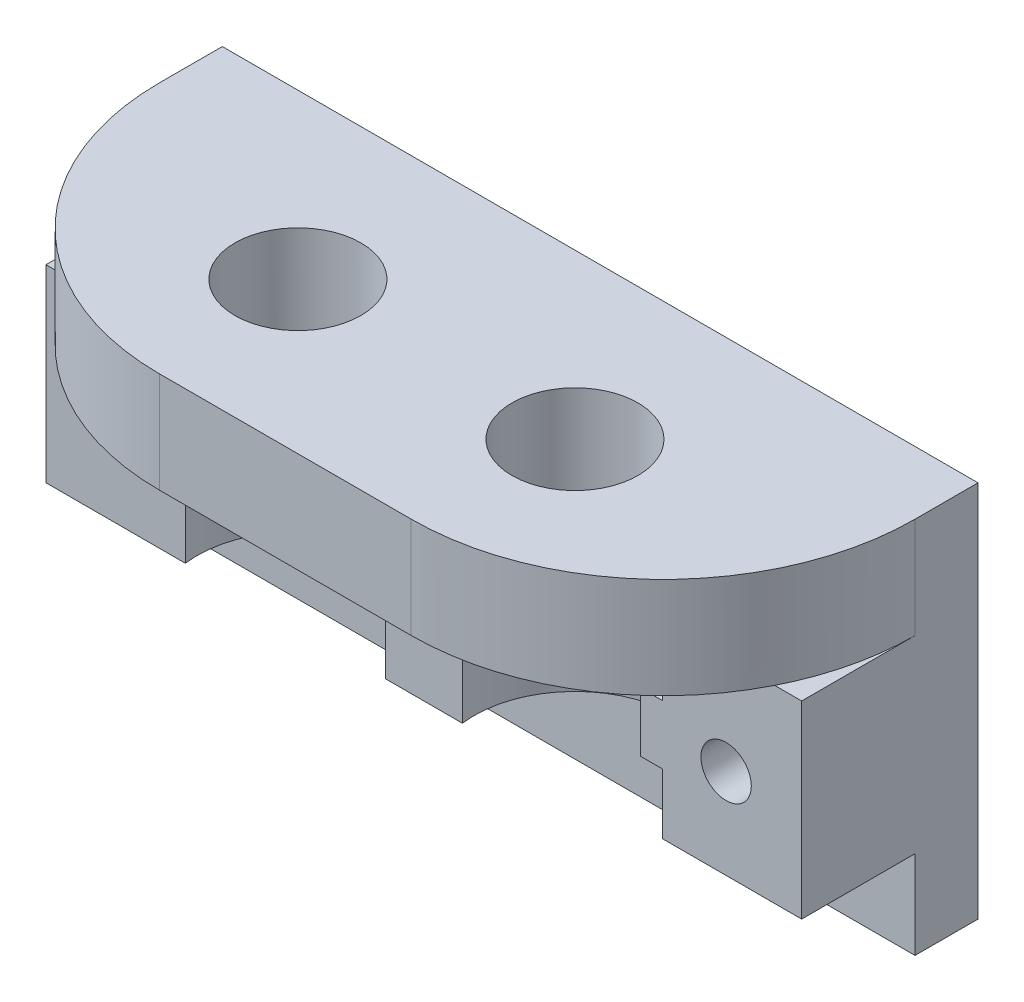
SolidWorks part; units mm, degrees
ref_plane "Piano frontale" through (0, 0, 0) normal (0, 0, 1) x (1, 0, 0)
ref_plane "Piano superiore" through (0, 0, 0) normal (0, 1, 0) x (1, 0, 0)
ref_plane "Piano destro" through (0, 0, 0) normal (1, 0, 0) x (0, 0, -1)
sketch "Schizzo1" plane through (0, 0, 0) normal (0, 0, 1) x (1, 0, 0)
  line L1 (-30, 15) -> (30, 15)
  line L2 (-30, 15) -> (-30, -15)
  line L3 (-30, -15) -> (30, -15)
  line L4 (30, 15) -> (30, -15)
  line L5 (-30, 15) -> (30, -15) construction
  line L6 (-30, -15) -> (30, 15) construction
  point P0 (0, 0)
  dimension "D1" = 60
  dimension "D2" = 30
extrude "Estrusione-Estrusione1" add sketch "Schizzo1" along normal blind 5
sketch "Schizzo2" plane through (0, 0, 5) normal (0, 0, 1) x (1, 0, 0)
  line L0 (-32.3459, -15) -> (49.5432, -15) construction
  line L1 (-32.3459, -8) -> (49.5432, -8) construction
  line L3 (30, -15) -> (30, 15) construction
  line L4 (-30, 15) -> (30, 15)
  line L5 (-30, 15) -> (-30, 7)
  line L6 (-30, 7) -> (30, 7)
  line L7 (30, 15) -> (30, 7)
  dimension "D1" = 7
extrude "Estrusione-Estrusione2" add sketch "Schizzo2" along normal blind 20
sketch "Schizzo3" plane through (0, 15, 0) normal (0, 1, 0) x (1, 0, 0)
  line L0 (0, 7.3603) -> (0, -33.3603) construction
  line L1 (11, 7.3603) -> (11, -33.3603) construction
  line L2 (30, 0) -> (-30, 0) construction
  circle A0 centre (11, -13) radius 5
  circle A1 centre (-11, -13) radius 5
  dimension "D2" = 10
  dimension "D3" = 13
  dimension "D1" = 11
extrude "Taglio-Estrusione1" cut sketch "Schizzo3" against normal up to surface (8 mm away) up to face at (-7.5, 7, 20)
fillet "Raccordo1" radius 20 2 edges at (30, 11, 25) (-30, 11, 25)
sketch "Schizzo4" plane through (0, 0, 5) normal (0, 0, 1) x (1, 0, 0)
  line L0 (-30, 7) -> (30, 7) construction
  line L1 (-30, 7) -> (30, 7)
  line L2 (-30, -8) -> (30, -8)
  line L3 (-30, -8) -> (-30, 7)
  line L4 (30, -8) -> (30, 7)
  dimension "D1" = 15
extrude "Estrusione-Estrusione3" add sketch "Schizzo4" along normal blind 10
sketch "Schizzo6" plane through (0, -8, 0) normal (0, -1, 0) x (1, 0, 0)
  line L0 (0, 28.7661) -> (0, -12.0233) construction
  line L1 (0, -7.3603) -> (0, 33.3603) construction
  circle A0 centre (-11, 13) radius 8
  circle A1 centre (11, 13) radius 8
  dimension "D1" = 16
extrude "Taglio-Estrusione2" cut sketch "Schizzo6" against normal blind 15
ref_plane "Piano1" through (-30, 7, 15) normal (0, -1, 0) x (-1, 0, 0)
sketch "Schizzo8" plane through (0, 0, 15) normal (0, 0, 1) x (1, 0, 0)
  line L1 (-30, 1.5) -> (-30, -3.2)
  line L3 (30, 1.5) -> (30, -3.2)
  line L4 (-30, 1.5) -> (30, 1.5)
  line L5 (-30, -3.2) -> (30, -3.2)
  line L8 (-31.6659, 1.5) -> (35.7067, 1.5) construction
  line L9 (-31.6659, -3.2) -> (35.7067, -3.2) construction
  dimension "D3" = 4.7
extrude "Estrusione-Estrusione4" add sketch "Schizzo8" against normal up to surface (10 mm away) up to face at (0, -10.3333, 5)
sketch "Schizzo9" plane through (0, -3.2, 0) normal (0, -1, 0) x (1, 0, 0)
  line L0 (0, 27.458) -> (0, -16.0891) construction
  line L1 (0, -7.3603) -> (0, 33.3603) construction
  circle A0 centre (-11, 13) radius 6.3
  circle A1 centre (11, 13) radius 6.3
extrude "Taglio-Estrusione3" cut sketch "Schizzo9" against normal blind 5
sketch "Schizzo10" plane through (0, 0, 15) normal (0, 0, 1) x (1, 0, 0)
  line L0 (-31.0418, -0.85) -> (32.2221, -0.85) construction
  circle A0 centre (0, -0.85) radius 2
  circle A1 centre (24, -0.85) radius 2
  circle A2 centre (-24, -0.85) radius 2
extrude "Taglio-Estrusione4" cut sketch "Schizzo10" against normal through all
sketch "Schizzo11" plane through (0, 0, 15) normal (0, 0, 1) x (1, 0, 0)
  line L1 (-30, 7) -> (30, 7)
  line L2 (-30, 7) -> (-30, -8)
  line L3 (-30, -8) -> (30, -8)
  line L4 (30, 7) -> (30, -8)
extrude "Taglio-Estrusione5" cut sketch "Schizzo11" against normal blind 1
